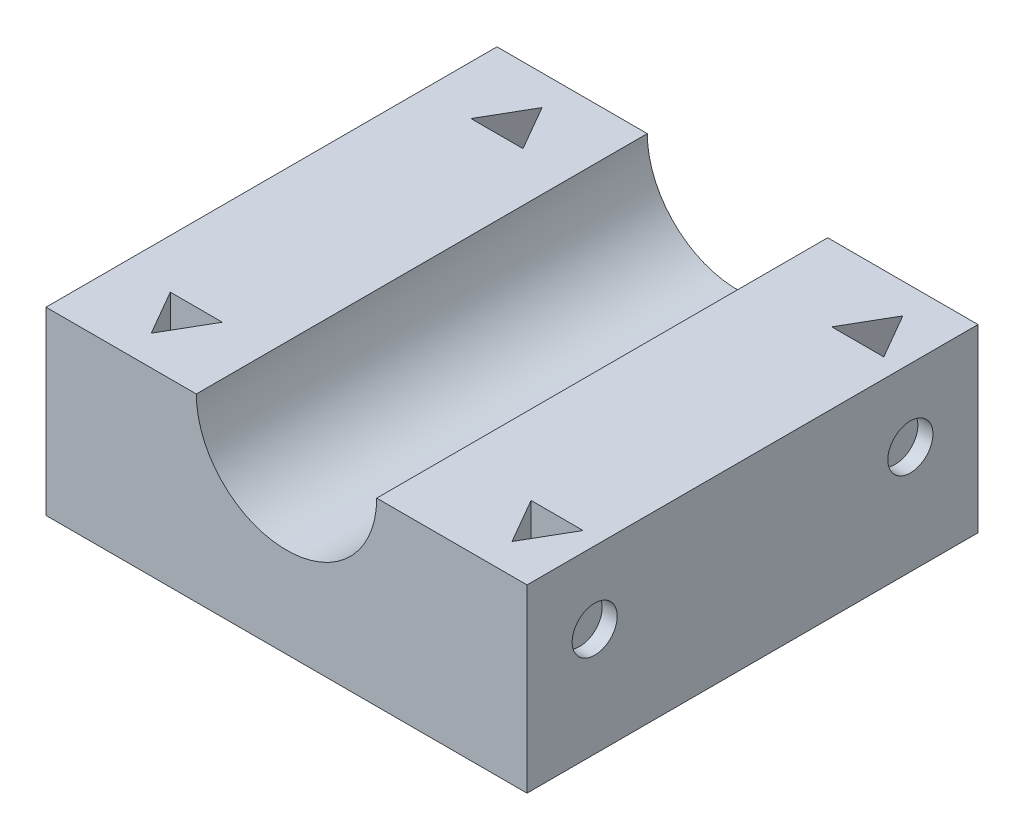
SolidWorks part; units mm, degrees
ref_plane "Front Plane" through (0, 0, 0) normal (0, 0, 1) x (1, 0, 0)
ref_plane "Top Plane" through (0, 0, 0) normal (0, 1, 0) x (1, 0, 0)
ref_plane "Right Plane" through (0, 0, 0) normal (1, 0, 0) x (0, 0, -1)
sketch "Sketch1" plane through (0, 0, 0) normal (0, 0, 1) x (1, 0, 0)
  line L0 (0, 0) -> (0, 12)
  line L1 (0, 12) -> (10, 12)
  line L2 (0, 0) -> (32, 0)
  line L3 (16, 6) -> (16, -29.5365) construction
  line L4 (32, 12) -> (22, 12)
  line L5 (32, 0) -> (32, 12)
  arc A0 (10, 12) -> (22, 12) centre (16, 12) ccw
  point P10 (16, 0)
  dimension "D3" = 6
  dimension "D4" = 12
  dimension "D5" = 16
  dimension "D1" = 12
  dimension "D2" = 10
extrude "Boss-Extrude1" add sketch "Sketch1" along normal blind 30
sketch "Sketch4" plane through (0, 12, 0) normal (0, 1, 0) x (1, 0, 0)
  line L1 (10, 0) -> (0, 0) construction
  line L2 (5, -2) -> (3.2679, -5)
  line L3 (3.2679, -5) -> (6.7321, -5)
  line L4 (6.7321, -5) -> (5, -2)
  line L5 (10, -30) -> (0, -30) construction
  line L6 (5, -28) -> (6.7321, -25)
  line L7 (6.7321, -25) -> (3.2679, -25)
  line L8 (3.2679, -25) -> (5, -28)
  line L10 (29, -28) -> (30.7321, -25)
  line L11 (30.7321, -25) -> (27.2679, -25)
  line L12 (27.2679, -25) -> (29, -28)
  line L13 (29, -2) -> (27.2679, -5)
  line L14 (27.2679, -5) -> (30.7321, -5)
  line L15 (30.7321, -5) -> (29, -2)
  circle A0 centre (5, -4) radius 1 construction
  circle A1 centre (5, -26) radius 1 construction
  circle A2 centre (29, -26) radius 1 construction
  circle A3 centre (29, -4) radius 1 construction
  dimension "D1" = 4
  dimension "D2" = 4
extrude "Cut-Extrude1" cut sketch "Sketch4" against normal through all
sketch "Sketch5" plane through (32, 0, 0) normal (1, 0, 0) x (0, 0, -1)
  line L0 (-30, 0) -> (0, 0) construction
  line L1 (-30, 0) -> (-30, 12) construction
  line L2 (-25.5, 7.2) -> (-4.5, 7.2) construction
  circle A0 centre (-25.5, 7.2) radius 1.5
  circle A1 centre (-4.5, 7.2) radius 1.5
  dimension "D1" = 7.2
  dimension "D2" = 4.5
  dimension "D3" = 21
extrude "Cut-Extrude2" cut sketch "Sketch5" against normal blind 1
sketch "Sketch6" plane through (0, 0, 0) normal (-1, 0, 0) x (0, 0, 1)
  line L2 (4.5, 7.6612) -> (25.5, 7.6612) construction
  line L3 (0, 12) -> (0, 0) construction
  circle A0 centre (4.5, 7.6612) radius 1.5
  circle A1 centre (25.5, 7.6612) radius 1.5
  dimension "D1" = 2
  dimension "D2" = 4.5
  dimension "D3" = 21
extrude "Cut-Extrude3" cut sketch "Sketch6" against normal blind 1
